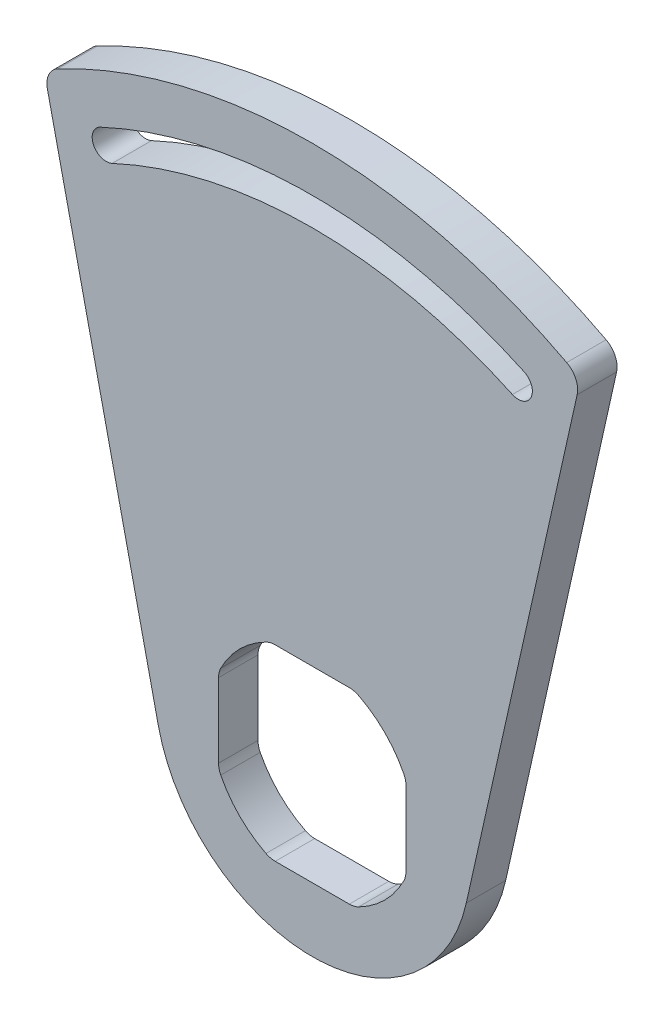
SolidWorks part; units mm, degrees
material "Delrin"
ref_plane "Front Plane" through (0, 0, 0) normal (0, 0, 1) x (1, 0, 0)
ref_plane "Top Plane" through (0, 0, 0) normal (0, 1, 0) x (1, 0, 0)
ref_plane "Right Plane" through (0, 0, 0) normal (1, 0, 0) x (0, 0, -1)
sketch "Sketch1" plane through (0, 0, 0) normal (0, 0, 1) x (1, 0, 0)
  line L0 (-24.7874, -5.5446) -> (-43.182, 76.6893)
  line L1 (24.7874, -5.5446) -> (43.182, 76.6893)
  line L2 (0, 0) -> (0, 78.486) construction
  line L3 (15.0876, -15.0876) -> (-15.0876, -15.0876)
  line L4 (15.0876, -15.0876) -> (15.0876, 15.0876)
  line L5 (15.0876, 15.0876) -> (-15.0876, 15.0876)
  line L6 (-15.0876, -15.0876) -> (-15.0876, 15.0876)
  line L7 (15.0876, -15.0876) -> (-15.0876, 15.0876) construction
  line L8 (15.0876, 15.0876) -> (-15.0876, -15.0876) construction
  arc A0 (-24.7874, -5.5446) -> (24.7874, -5.5446) centre (0, 0) ccw
  arc A1 (-43.182, 76.6893) -> (43.182, 76.6893) centre (0, 0) cw
  circle A2 centre (0, 0) radius 16.51
  arc A3 (-33.1696, 71.1325) -> (33.1696, 71.1325) centre (0, 0) cw construction
  arc A4 (34.125, 73.1813) -> (-34.125, 73.1813) centre (0, 0) ccw
  arc A5 (32.2142, 69.0837) -> (-32.2142, 69.0837) centre (0, 0) ccw
  arc A6 (32.2142, 69.0837) -> (34.125, 73.1813) centre (33.1696, 71.1325) ccw
  arc A7 (-34.125, 73.1813) -> (-32.2142, 69.0837) centre (-33.1696, 71.1325) ccw
  point P6 (0, 88.011)
  point P14 (0, 78.486)
  point P19 (-35.2184, 70.1771)
extrude "Boss-Extrude1" add sketch "Sketch1" along normal blind 6.35 contours A1 L0 A0 L1 A2 L5 L4 L3 L6 | L6 A2 | L5 A2 | L3 A2 | L4 A2 | A2 L5 L6 | A2 L4 L5 | A2 L3 L4 | A2 L6 L3
sketch "Sketch2" plane through (0, 0, 6.35) normal (0, 0, 1) x (1, 0, 0)
  circle A0 centre (0, 0) radius 17.78
  dimension "D1" = 35.56
extrude "Cut-Extrude1" [suppressed] cut sketch "Sketch2" against normal blind 0.508
fillet "Fillet1" radius 3.302 8 edges at (6.7041, 15.0876, 3.175) (-6.7041, 15.0876, 3.175) (15.0876, -6.7041, 3.175) (15.0876, 6.7041, 3.175) (-6.7041, -15.0876, 3.175) (6.7041, -15.0876, 3.175) (-15.0876, 6.7041, 3.175) (-15.0876, -6.7041, 3.175)
fillet "Fillet2" radius 3.302 2 edges at (43.182, 76.6893, 3.175) (-43.182, 76.6893, 3.175)
equation "\"D4@Sketch1\"=\"D7@Sketch1\"+.375"
